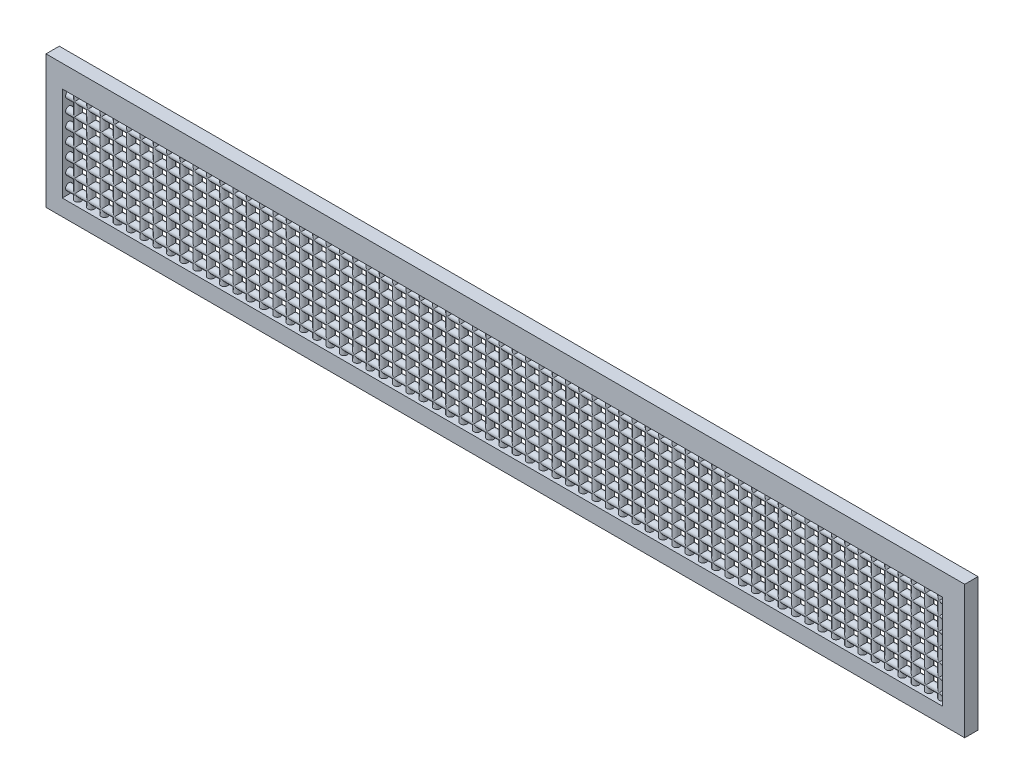
SolidWorks part; units mm, degrees
ref_plane "Front Plane" through (0, 0, 0) normal (0, 0, 1) x (1, 0, 0)
ref_plane "Top Plane" through (0, 0, 0) normal (0, 1, 0) x (1, 0, 0)
ref_plane "Right Plane" through (0, 0, 0) normal (1, 0, 0) x (0, 0, -1)
sketch "Sketch2" plane through (0, 0, 0) normal (0, 0, 1) x (1, 0, 0)
  line L0 (-25.1988, 31.651) -> (-25.1988, 35.651)
  line L1 (-42.4688, 36.151) -> (-7.9288, 36.151)
  line L2 (-42.4688, 36.151) -> (-42.4688, 31.151)
  line L3 (-42.4688, 31.151) -> (-7.9288, 31.151)
  line L4 (-7.9288, 36.151) -> (-7.9288, 31.151)
  line L5 (-41.9688, 35.651) -> (-8.4288, 35.651)
  line L6 (-41.9688, 35.651) -> (-41.9688, 31.651)
  line L7 (-41.9688, 31.651) -> (-8.4288, 31.651)
  line L8 (-8.4288, 35.651) -> (-8.4288, 31.651)
  line L9 (-24.6988, 31.651) -> (-24.6988, 35.651)
  line L10 (-24.1988, 31.651) -> (-24.1988, 35.651)
  line L11 (-23.6988, 31.651) -> (-23.6988, 35.651)
  line L12 (-23.1988, 31.651) -> (-23.1988, 35.651)
  line L13 (-22.6988, 31.651) -> (-22.6988, 35.651)
  line L14 (-22.1988, 31.651) -> (-22.1988, 35.651)
  line L15 (-21.6988, 31.651) -> (-21.6988, 35.651)
  line L16 (-21.1988, 31.651) -> (-21.1988, 35.651)
  line L17 (-20.6988, 31.651) -> (-20.6988, 35.651)
  line L18 (-20.1988, 31.651) -> (-20.1988, 35.651)
  line L19 (-19.6988, 31.651) -> (-19.6988, 35.651)
  line L20 (-19.1988, 31.651) -> (-19.1988, 35.651)
  line L21 (-18.6988, 31.651) -> (-18.6988, 35.651)
  line L22 (-18.1988, 31.651) -> (-18.1988, 35.651)
  line L23 (-17.6988, 31.651) -> (-17.6988, 35.651)
  line L24 (-17.1988, 31.651) -> (-17.1988, 35.651)
  line L25 (-16.6988, 31.651) -> (-16.6988, 35.651)
  line L26 (-16.1988, 31.651) -> (-16.1988, 35.651)
  line L27 (-15.6988, 31.651) -> (-15.6988, 35.651)
  line L28 (-15.1988, 31.651) -> (-15.1988, 35.651)
  line L29 (-14.6988, 31.651) -> (-14.6988, 35.651)
  line L30 (-14.1988, 31.651) -> (-14.1988, 35.651)
  line L31 (-13.6988, 31.651) -> (-13.6988, 35.651)
  line L32 (-13.1988, 31.651) -> (-13.1988, 35.651)
  line L33 (-12.6988, 31.651) -> (-12.6988, 35.651)
  line L34 (-12.1988, 31.651) -> (-12.1988, 35.651)
  line L35 (-11.6988, 31.651) -> (-11.6988, 35.651)
  line L36 (-11.1988, 31.651) -> (-11.1988, 35.651)
  line L37 (-10.6988, 31.651) -> (-10.6988, 35.651)
  line L38 (-10.1988, 31.651) -> (-10.1988, 35.651)
  line L39 (-9.6988, 31.651) -> (-9.6988, 35.651)
  line L40 (-9.1988, 31.651) -> (-9.1988, 35.651)
  line L41 (-8.6988, 31.651) -> (-8.6988, 35.651)
  line L42 (-25.6988, 31.651) -> (-25.6988, 35.651)
  line L43 (-26.1988, 31.651) -> (-26.1988, 35.651)
  line L44 (-26.6988, 31.651) -> (-26.6988, 35.651)
  line L45 (-27.1988, 31.651) -> (-27.1988, 35.651)
  line L46 (-27.6988, 31.651) -> (-27.6988, 35.651)
  line L47 (-28.1988, 31.651) -> (-28.1988, 35.651)
  line L48 (-28.6988, 31.651) -> (-28.6988, 35.651)
  line L49 (-29.1988, 31.651) -> (-29.1988, 35.651)
  line L50 (-29.6988, 31.651) -> (-29.6988, 35.651)
  line L51 (-30.1988, 31.651) -> (-30.1988, 35.651)
  line L52 (-30.6988, 31.651) -> (-30.6988, 35.651)
  line L53 (-31.1988, 31.651) -> (-31.1988, 35.651)
  line L54 (-31.6988, 31.651) -> (-31.6988, 35.651)
  line L55 (-32.1988, 31.651) -> (-32.1988, 35.651)
  line L56 (-32.6988, 31.651) -> (-32.6988, 35.651)
  line L57 (-33.1988, 31.651) -> (-33.1988, 35.651)
  line L58 (-33.6988, 31.651) -> (-33.6988, 35.651)
  line L59 (-34.1988, 31.651) -> (-34.1988, 35.651)
  line L60 (-34.6988, 31.651) -> (-34.6988, 35.651)
  line L61 (-35.1988, 31.651) -> (-35.1988, 35.651)
  line L62 (-35.6988, 31.651) -> (-35.6988, 35.651)
  line L63 (-36.1988, 31.651) -> (-36.1988, 35.651)
  line L64 (-36.6988, 31.651) -> (-36.6988, 35.651)
  line L65 (-37.1988, 31.651) -> (-37.1988, 35.651)
  line L66 (-37.6988, 31.651) -> (-37.6988, 35.651)
  line L67 (-38.1988, 31.651) -> (-38.1988, 35.651)
  line L68 (-38.6988, 31.651) -> (-38.6988, 35.651)
  line L69 (-39.1988, 31.651) -> (-39.1988, 35.651)
  line L70 (-39.6988, 31.651) -> (-39.6988, 35.651)
  line L71 (-40.1988, 31.651) -> (-40.1988, 35.651)
  line L72 (-40.6988, 31.651) -> (-40.6988, 35.651)
  line L73 (-41.1988, 31.651) -> (-41.1988, 35.651)
  line L74 (-41.6988, 31.651) -> (-41.6988, 35.651)
  line L75 (-41.4688, 31.651) -> (-8.4288, 31.651)
  line L76 (-41.4688, 32.151) -> (-8.4288, 32.151)
  line L77 (-41.4688, 32.651) -> (-8.4288, 32.651)
  line L78 (-41.4688, 33.151) -> (-8.4288, 33.151)
  line L79 (-41.4688, 33.651) -> (-8.4288, 33.651)
  line L80 (-41.4688, 34.151) -> (-8.4288, 34.151)
  line L81 (-41.4688, 34.651) -> (-8.4288, 34.651)
  line L82 (-41.4688, 35.151) -> (-8.4288, 35.151)
  line L83 (-41.4688, 35.651) -> (-8.4288, 35.651)
  line L84 (-41.4688, 36.151) -> (-7.9288, 36.151)
  line L85 (-41.9688, 32.151) -> (-8.4288, 32.151)
  line L86 (-41.9688, 32.651) -> (-8.4288, 32.651)
  line L87 (-41.9688, 33.151) -> (-8.4288, 33.151)
  line L88 (-41.9688, 33.651) -> (-8.4288, 33.651)
  line L89 (-41.9688, 34.151) -> (-8.4288, 34.151)
  line L90 (-41.9688, 34.651) -> (-8.4288, 34.651)
  line L91 (-41.9688, 35.151) -> (-8.4288, 35.151)
  line L92 (-41.9688, 35.651) -> (-8.4288, 35.651)
  line L93 (-41.9688, 36.151) -> (-8.4288, 36.151)
  dimension "D1" = 5
  dimension "D2" = 34.54
  dimension "D3" = 0.5
  dimension "D4" = 0.5
  dimension "D5" = 0.5
  dimension "D6" = 0.5
  dimension "D7" = 16.77
  dimension "D8" = 16.77
  dimension "D9" = 34
  dimension "D10" = 34
  dimension "D11" = 2
  dimension "D12" = 10
extrude "Boss-Extrude2" add sketch "Sketch2" along normal blind 0.5 contours L1 L4 L3 L2
sketch "Sketch5" plane through (0, 0, 0.5) normal (0, 0, 1) x (1, 0, 0)
  line L1 (-8.7656, 31.7627) -> (-41.8567, 31.7627)
  line L2 (-8.7656, 31.7627) -> (-8.7656, 35.3146)
  line L3 (-8.7656, 35.3146) -> (-41.8567, 35.3146)
  line L4 (-41.8567, 31.7627) -> (-41.8567, 35.3146)
extrude "Cut-Extrude1" cut sketch "Sketch5" against normal blind 1
sketch "Sketch7" plane through (0, 31.7627, 0) normal (0, 1, 0) x (1, 0, 0)
  line L0 (-41.8567, -0.5) -> (-8.7656, -0.5) construction
  line L1 (-8.7656, 0) -> (-8.7656, -0.5) construction
  circle A0 centre (-9.0156, -0.25) radius 0.125
  dimension "D1" = 0.25
  dimension "D2" = 0.25
  dimension "D3" = 0.25
extrude "Boss-Extrude4" add sketch "Sketch7" along normal blind 3.55
pattern_linear "LPattern2" count 66 spacing 0.5 along (-1, 0, 0) of "Boss-Extrude4"
sketch "Sketch8" plane through (-8.7656, 0, 0) normal (-1, 0, 0) x (0, 0, 1)
  line L0 (0, 31.7627) -> (0, 35.3146) construction
  line L1 (0, 31.7627) -> (0.5, 31.7627) construction
  circle A0 centre (0.25, 32.0127) radius 0.125
  point P2 (0, 0)
  dimension "D1" = 0.25
  dimension "D2" = 0.25
  dimension "D3" = 0.25
extrude "Boss-Extrude5" add sketch "Sketch8" along normal blind 33.1
pattern_linear "LPattern3" count 7 spacing 0.5 along (0, 1, 0) of "Boss-Extrude5"
